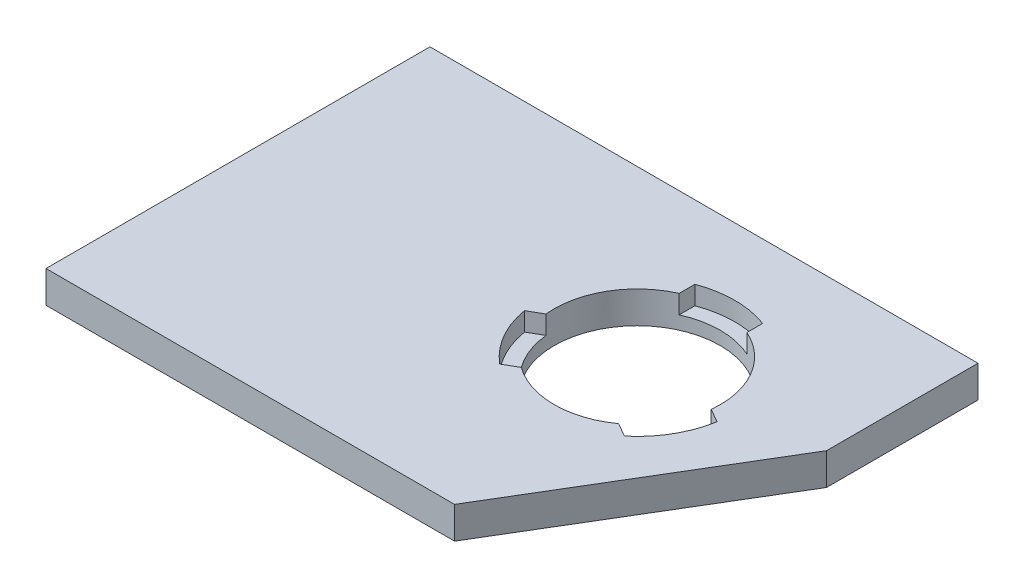
SolidWorks part; units mm, degrees
ref_plane "Front Plane" through (0, 0, 0) normal (0, 0, 1) x (1, 0, 0)
ref_plane "Top Plane" through (0, 0, 0) normal (0, 1, 0) x (1, 0, 0)
ref_plane "Right Plane" through (0, 0, 0) normal (1, 0, 0) x (0, 0, -1)
sketch "Sketch1" plane through (0, 0, 0) normal (0, 1, 0) x (1, 0, 0)
  line L1 (-20.3661, -10.164) -> (62.1339, -10.164)
  line L2 (-20.3661, -10.164) -> (-20.3661, 47.636)
  line L3 (-20.3661, 47.636) -> (62.1339, 47.636)
  line L4 (62.1339, -10.164) -> (62.1339, 47.636)
  dimension "D1" = 82.5
  dimension "D2" = 57.8
extrude "Boss-Extrude1" add sketch "Sketch1" along normal blind 4.8
sketch "Sketch2" plane through (0, 4.8, 0) normal (0, 1, 0) x (1, 0, 0)
  line L0 (41.1339, -10.164) -> (62.1339, 24.836)
  line L1 (-20.3661, -10.164) -> (62.1339, -10.164) construction
  line L2 (62.1339, -10.164) -> (62.1339, 47.636) construction
  line L3 (62.1339, 24.836) -> (62.1339, -10.164)
  line L4 (62.1339, -10.164) -> (41.1339, -10.164)
  circle A0 centre (35.6339, 22.836) radius 12.5
  dimension "D3" = 25
  dimension "D1" = 35
  dimension "D2" = 21
  dimension "D4" = 26.5
  dimension "D5" = 33
extrude "Cut-Extrude1" cut sketch "Sketch2" against normal blind 4.8
sketch "Sketch3" plane through (0, 4.8, 0) normal (0, 1, 0) x (1, 0, 0)
  line L0 (-20.3661, -10.164) -> (41.1339, -10.164) construction
  line L1 (62.1339, 24.836) -> (62.1339, 47.636) construction
  line L2 (35.6339, 22.836) -> (35.6339, 37.536)
  line L3 (35.6339, 22.836) -> (22.9033, 15.486)
  line L4 (35.6339, 22.836) -> (48.3645, 15.486)
  line L5 (35.6339, 37.536) -> (40.7339, 37.536)
  line L10 (40.7339, 37.536) -> (40.7339, 31.536)
  line L11 (40.7339, 31.536) -> (30.5339, 31.536)
  line L12 (30.5339, 31.536) -> (30.5339, 37.536)
  line L13 (30.5339, 37.536) -> (35.6339, 37.536)
  line L14 (48.3645, 15.486) -> (45.8145, 11.0693)
  line L15 (45.8145, 11.0693) -> (40.6183, 14.0693)
  line L16 (40.6183, 14.0693) -> (45.7183, 22.9027)
  line L17 (45.7183, 22.9027) -> (50.9145, 19.9027)
  line L18 (50.9145, 19.9027) -> (48.3645, 15.486)
  line L19 (22.9033, 15.486) -> (20.3533, 19.9027)
  line L20 (20.3533, 19.9027) -> (25.5495, 22.9027)
  line L21 (25.5495, 22.9027) -> (30.6495, 14.0693)
  line L22 (30.6495, 14.0693) -> (25.4533, 11.0693)
  line L23 (25.4533, 11.0693) -> (22.9033, 15.486)
  circle A0 centre (35.6339, 22.836) radius 14.7
  circle M23 centre (35.6339, 22.836) radius 12.5
  dimension "D1" = 29.4
  dimension "D2" = 33
  dimension "D3" = 26.5
  dimension "D4" = 120
  dimension "D5" = 120
  dimension "D6" = 5.1
  dimension "D7" = 5.1
  dimension "D8" = 6
  dimension "D9" = 3
extrude "Cut-Extrude2" cut sketch "Sketch3" against normal blind 2.8 contours L2 A0 L12 M23 | L10 A0 L2 M23 | L4 A0 L17 M23 | L15 A0 L4 M23 | L20 A0 L3 M23 | L3 A0 L22 M23
